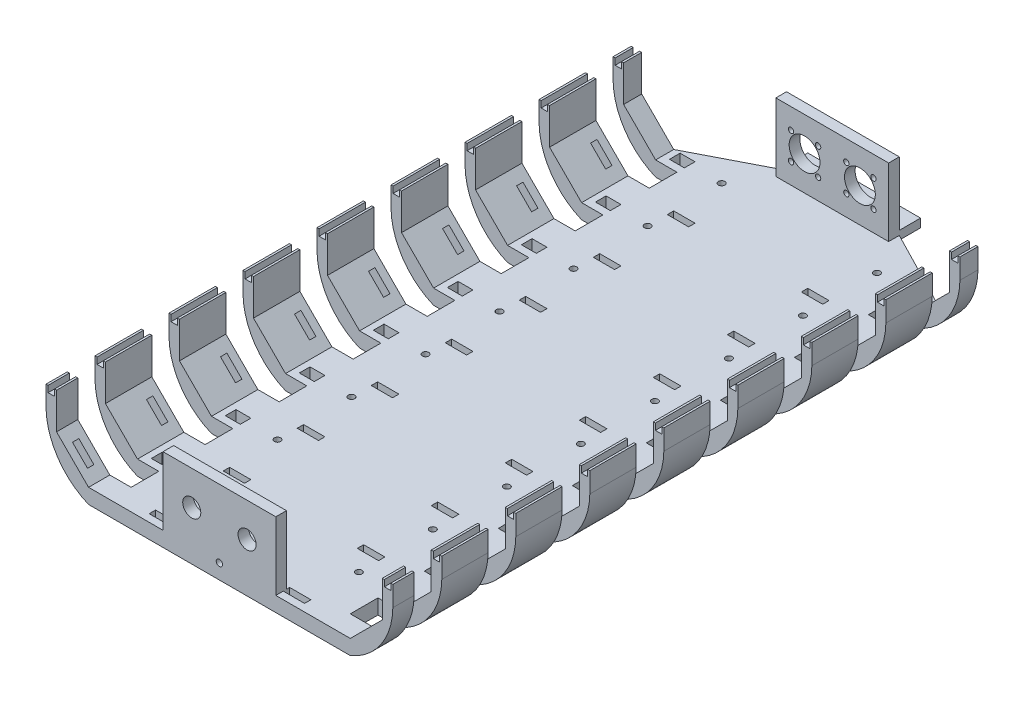
SolidWorks part; units mm, degrees
ref_plane "Front Plane" through (0, 0, 0) normal (0, 0, 1) x (1, 0, 0)
ref_plane "Top Plane" through (0, 0, 0) normal (0, 1, 0) x (1, 0, 0)
ref_plane "Right Plane" through (0, 0, 0) normal (1, 0, 0) x (0, 0, -1)
sketch "Sketch1" plane through (0, 0, 0) normal (0, 1, 0) x (1, 0, 0)
  line L0 (0, -135) -> (0, 135) construction
  line L1 (-13, 135) -> (-36, 135)
  line L2 (13, -135) -> (-13, -135)
  line L3 (13, -135) -> (13, 135) construction
  line L4 (13, 135) -> (-13, 135)
  line L5 (-13, -135) -> (-13, 135) construction
  line L8 (-36, 135) -> (-36, -135) construction
  line L9 (-36, -135) -> (-13, -135)
  line L10 (-36, 135) -> (-61.5, 135)
  line L11 (-61.5, 135) -> (-61.5, -135)
  line L12 (-61.5, -135) -> (-36, -135)
  line L13 (36, -135) -> (13, -135)
  line L14 (61.5, -135) -> (36, -135)
  line L15 (61.5, 135) -> (61.5, -135)
  line L16 (36, 135) -> (36, -135) construction
  line L17 (13, 135) -> (36, 135)
  line L18 (36, 135) -> (61.5, 135)
  point P0 (0, 0)
  point P4 (0, 0)
  dimension "D1" = 270
  dimension "D2" = 26
  dimension "D3" = 23
  dimension "D4" = 123
extrude "Boss-Extrude1" add sketch "Sketch1" along normal blind 7
sketch "Sketch2" plane through (0, 7, 0) normal (0, 1, 0) x (1, 0, 0)
  line L0 (61.5, -135) -> (61.5, 135) construction
  line L1 (-61.5, -135) -> (61.5, -135)
  line L2 (-61.5, -135) -> (-61.5, -130)
  line L3 (-61.5, -130) -> (61.5, -130)
  line L4 (61.5, -135) -> (61.5, -130)
  line L21 (-26.5, 130) -> (-26.5, -130) construction
  dimension "D1" = 5
extrude "Boss-Extrude2" add sketch "Sketch2" along normal blind 32
sketch "Sketch3" plane through (0, 0, 135) normal (0, 0, 1) x (1, 0, 0)
  line L0 (0, 39) -> (0, 0) construction
  line L2 (-61.5, 39) -> (-61.5, 7) construction
  line L3 (-61.5, 39) -> (61.5, 39) construction
  line L5 (-61.5, 39) -> (-61.5, 0) construction
  line L6 (-61.5, 23) -> (61.5, 23) construction
  line L7 (61.5, 39) -> (61.5, 0) construction
  circle A0 centre (-13, 23) radius 4.25
  circle A1 centre (13, 23) radius 4.25
  dimension "D1" = 8.5
  dimension "D2" = 8.5
  dimension "D3" = 26
  dimension "D4" = 13
  dimension "D5" = 32
  dimension "D6" = 16
sketch "Sketch9" plane through (0, 0, -135) normal (0, 0, -1) x (-1, 0, 0)
  line L1 (-61.5, 7) -> (61.5, 7)
  line L2 (-61.5, 7) -> (-61.5, 0)
  line L3 (-61.5, 0) -> (61.5, 0)
  line L4 (61.5, 7) -> (61.5, 0)
extrude "Boss-Extrude4" add sketch "Sketch9" along normal blind 5
sketch "Sketch13" plane through (0, 0, 135) normal (0, 0, 1) x (1, 0, 0)
  line L0 (-61.5, 39) -> (-61.5, 7)
  line L1 (-61.5, 39) -> (-61.5, 0) construction
  line L2 (-61.5, 39) -> (-26.5, 39)
  line L3 (-61.5, 39) -> (61.5, 39) construction
  line L4 (-26.5, 39) -> (-26.5, 7)
  line L5 (-26.5, 7) -> (-61.5, 7)
  line L6 (0, 39) -> (0, 5.5161) construction
  line L7 (26.5, 39) -> (26.5, 7)
  line L8 (61.5, 39) -> (26.5, 39)
  line L9 (61.5, 39) -> (61.5, 7)
  line L10 (26.5, 7) -> (61.5, 7)
  dimension "D1" = 32
  dimension "D2" = 35
extrude "Cut-Extrude5" cut sketch "Sketch13" against normal blind 11
sketch "Sketch14" plane through (0, 0, 135) normal (0, 0, 1) x (1, 0, 0)
  line L0 (0, 39) -> (0, 0) construction
  line L1 (-26.5, 39) -> (26.5, 39) construction
  line L2 (-81.5, 39) -> (0, 39) construction
  line L3 (-61.5, 0) -> (-81.5, 20) construction
  line L5 (-76.55, 22.05) -> (-61.5, 7)
  line L6 (-61.5, 0) -> (61.5, 0) construction
  line L7 (-61.5, 7) -> (-61.5, 0)
  line L12 (-81.5, 20) -> (-81.5, 39) construction
  line L13 (-81.5, 39) -> (-76.55, 39)
  line L14 (-76.55, 39) -> (-76.55, 22.05)
  line L21 (-61.5, 7) -> (-61.5, 39) construction
  line L22 (-81.5, 39) -> (-81.5, 29.5)
  line L23 (81.5, 39) -> (76.55, 39)
  line L24 (76.55, 39) -> (76.55, 22.05)
  line L25 (76.55, 22.05) -> (61.5, 7)
  line L26 (61.5, 7) -> (61.5, 0)
  line L27 (81.5, 39) -> (81.5, 29.5)
  arc A0 (-61.5, 0) -> (-81.5, 29.5) centre (-49.0062, 30) cw
  arc A1 (61.5, 0) -> (81.5, 29.5) centre (49.0062, 30) ccw
  dimension "D1" = 28.2843
  dimension "D2" = 45
  dimension "D3" = 4.95
  dimension "D4" = 20
  dimension "D5" = 4.9497
  dimension "D6" = 21.2839
  dimension "D7" = 30
  dimension "D8" = 9.5
extrude "Boss-Extrude10" add sketch "Sketch14" against normal blind 275
sketch "Sketch17" plane through (0, 7, 0) normal (0, 1, 0) x (1, 0, 0)
  line L0 (-26.5, 130) -> (26.5, 130) construction
  line L1 (0, 130) -> (0, 161) construction
  line L2 (-26.5, -135) -> (-26.5, 161) construction
  line L3 (26.5, -135) -> (26.5, 161) construction
  line L4 (26.5, 161) -> (-26.5, 161) construction
  line L5 (0, 161) -> (0, 226) construction
  line L6 (-61.5, 140) -> (-26.5, 226)
  line L7 (-26.5, 226) -> (0, 226)
  line L8 (0, 226) -> (26.5, 226)
  line L9 (26.5, 226) -> (61.5, 140)
  line L10 (26.5, 161) -> (26.5, 226) construction
  line L11 (-26.5, 161) -> (-26.5, 226) construction
  line L12 (-61.5, 140) -> (61.5, 140)
  line L13 (-61.5, 140) -> (61.5, 140) construction
  dimension "D1" = 31
  dimension "D2" = 296
  dimension "D3" = 90
  dimension "D4" = 65
  dimension "D5" = 10
extrude "Boss-Extrude13" add sketch "Sketch17" against normal blind 7 contours L12 L9 L8 L7 L6
sketch "Sketch18" plane through (0, 7, 0) normal (0, 1, 0) x (1, 0, 0)
  line L0 (-26.5, 127) -> (26.5, 127) construction
  line L1 (0, 127) -> (0, 158) construction
  line L2 (-26.5, 135) -> (-26.5, 158) construction
  line L3 (26.5, 132) -> (26.5, 158) construction
  line L4 (-26.5, 158) -> (-26.5, 153)
  line L5 (-26.5, 153) -> (26.5, 153)
  line L6 (26.5, 153) -> (26.5, 158)
  line L7 (26.5, 158) -> (-26.5, 158)
  line L8 (-61.5, 140) -> (-61.5, -135) construction
  line L9 (76.55, 140) -> (61.5, 140) construction
  dimension "D1" = 31
  dimension "D2" = 5
  dimension "D3" = 35
  dimension "D4" = 53
  dimension "D5" = 13
extrude "Boss-Extrude14" add sketch "Sketch18" along normal blind 32
extrude "Cut-Extrude8" cut sketch "Sketch3" against normal blind 334
sketch "Sketch19" plane through (0, 0, -153) normal (0, 0, 1) x (1, 0, 0)
  line L0 (0, 39) -> (0, 0) construction
  line L1 (-26.5, 39) -> (26.5, 39) construction
  line L3 (-6.636, 16.636) -> (-19.364, 16.636) construction
  line L4 (-6.636, 16.636) -> (-6.636, 29.364) construction
  line L5 (-6.636, 29.364) -> (-19.364, 29.364) construction
  line L6 (-19.364, 16.636) -> (-19.364, 29.364) construction
  line L7 (-6.636, 16.636) -> (-19.364, 29.364) construction
  line L8 (-6.636, 29.364) -> (-19.364, 16.636) construction
  circle A0 centre (-13, 23) radius 7.25
  circle A1 centre (-6.636, 16.636) radius 1.25
  circle A2 centre (-6.636, 29.364) radius 1.25
  circle A3 centre (-19.364, 29.364) radius 1.25
  circle A4 centre (-19.364, 16.636) radius 1.25
  circle A5 centre (13, 23) radius 7.25
  circle A6 centre (19.364, 16.636) radius 1.25
  circle A7 centre (6.636, 16.636) radius 1.25
  circle A8 centre (6.636, 29.364) radius 1.25
  circle A9 centre (19.364, 29.364) radius 1.25
  dimension "D1" = 14.5
  dimension "D4" = 2.5
  dimension "D5" = 2.5
  dimension "D6" = 2.5
  dimension "D7" = 2.5
  dimension "D2" = 18
  dimension "D3" = 18
  dimension "D8" = 12.7279
extrude "Cut-Extrude9" cut sketch "Sketch19" against normal blind 334
sketch "Sketch29" plane through (0, 7, 0) normal (0, 1, 0) x (1, 0, 0)
  line L0 (-61.5, 140) -> (-26.5, 158)
  line L1 (-26.5, 158) -> (26.5, 158)
  line L2 (26.5, 158) -> (61.5, 140)
  line L3 (61.5, 140) -> (26.5, 226)
  line L4 (26.5, 226) -> (-26.5, 226)
  line L5 (-26.5, 226) -> (-61.5, 140)
extrude "Cut-Extrude13" cut sketch "Sketch29" against normal blind 19
sketch "Sketch32" plane through (0, 7, 0) normal (0, 1, 0) x (1, 0, 0)
  line L0 (-61.5, 137.5) -> (-55, 137.5) construction
  line L1 (-61.5, 140) -> (-26.5, 140) construction
  line L3 (-61.5, 140) -> (-61.5, 130) construction
  line L4 (0, 158) -> (0, -135) construction
  line L5 (26.5, 158) -> (-26.5, 158) construction
  line L6 (-26.5, -135) -> (26.5, -135) construction
  line L7 (-61.5, 130) -> (-26.5, 130) construction
  line L8 (-81.5, 131.5) -> (-51.5, 131.5)
  line L9 (-26.5, 140) -> (-26.5, 130) construction
  line L10 (-81.5, 131.5) -> (-81.5, 118.5)
  line L11 (-51.5, 135) -> (-58.5, 135)
  line L12 (-51.5, 135) -> (-51.5, 140)
  line L13 (-51.5, 140) -> (-58.5, 140)
  line L14 (-58.5, 135) -> (-58.5, 140)
  line L15 (-51.5, 135) -> (-58.5, 140) construction
  line L16 (-51.5, 140) -> (-58.5, 135) construction
  line L23 (-81.5, 118.5) -> (-51.5, 118.5)
  line L24 (-51.5, 131.5) -> (-51.5, 118.5)
  line L25 (-81.5, 96.7143) -> (-81.5, 83.7143)
  line L26 (-81.5, 96.7143) -> (-51.5, 96.7143)
  line L27 (-51.5, 96.7143) -> (-51.5, 83.7143)
  line L28 (-81.5, 83.7143) -> (-51.5, 83.7143)
  line L29 (-51.5, 100.2143) -> (-51.5, 105.2143)
  line L30 (-51.5, 100.2143) -> (-58.5, 100.2143)
  line L31 (-58.5, 100.2143) -> (-58.5, 105.2143)
  line L32 (-51.5, 105.2143) -> (-58.5, 105.2143)
  line L37 (-81.5, 61.9286) -> (-81.5, 48.9286)
  line L38 (-81.5, 61.9286) -> (-51.5, 61.9286)
  line L39 (-51.5, 61.9286) -> (-51.5, 48.9286)
  line L40 (-81.5, 48.9286) -> (-51.5, 48.9286)
  line L41 (-51.5, 65.4286) -> (-51.5, 70.4286)
  line L42 (-51.5, 65.4286) -> (-58.5, 65.4286)
  line L43 (-58.5, 65.4286) -> (-58.5, 70.4286)
  line L44 (-51.5, 70.4286) -> (-58.5, 70.4286)
  line L49 (-81.5, 27.1429) -> (-81.5, 14.1429)
  line L50 (-81.5, 27.1429) -> (-51.5, 27.1429)
  line L51 (-51.5, 27.1429) -> (-51.5, 14.1429)
  line L52 (-81.5, 14.1429) -> (-51.5, 14.1429)
  line L53 (-51.5, 30.6429) -> (-51.5, 35.6429)
  line L54 (-51.5, 30.6429) -> (-58.5, 30.6429)
  line L55 (-58.5, 30.6429) -> (-58.5, 35.6429)
  line L56 (-51.5, 35.6429) -> (-58.5, 35.6429)
  line L61 (-81.5, -7.6429) -> (-81.5, -20.6429)
  line L62 (-81.5, -7.6429) -> (-51.5, -7.6429)
  line L63 (-51.5, -7.6429) -> (-51.5, -20.6429)
  line L64 (-81.5, -20.6429) -> (-51.5, -20.6429)
  line L65 (-51.5, -4.1429) -> (-51.5, 0.8571)
  line L66 (-51.5, -4.1429) -> (-58.5, -4.1429)
  line L67 (-58.5, -4.1429) -> (-58.5, 0.8571)
  line L68 (-51.5, 0.8571) -> (-58.5, 0.8571)
  line L73 (-81.5, -42.4286) -> (-81.5, -55.4286)
  line L74 (-81.5, -42.4286) -> (-51.5, -42.4286)
  line L75 (-51.5, -42.4286) -> (-51.5, -55.4286)
  line L76 (-81.5, -55.4286) -> (-51.5, -55.4286)
  line L77 (-51.5, -38.9286) -> (-51.5, -33.9286)
  line L78 (-51.5, -38.9286) -> (-58.5, -38.9286)
  line L79 (-58.5, -38.9286) -> (-58.5, -33.9286)
  line L80 (-51.5, -33.9286) -> (-58.5, -33.9286)
  line L85 (-81.5, -77.2143) -> (-81.5, -90.2143)
  line L86 (-81.5, -77.2143) -> (-51.5, -77.2143)
  line L87 (-51.5, -77.2143) -> (-51.5, -90.2143)
  line L88 (-81.5, -90.2143) -> (-51.5, -90.2143)
  line L89 (-51.5, -73.7143) -> (-51.5, -68.7143)
  line L90 (-51.5, -73.7143) -> (-58.5, -73.7143)
  line L91 (-58.5, -73.7143) -> (-58.5, -68.7143)
  line L92 (-51.5, -68.7143) -> (-58.5, -68.7143)
  line L97 (-81.5, -112) -> (-81.5, -125)
  line L98 (-81.5, -112) -> (-51.5, -112)
  line L99 (-51.5, -112) -> (-51.5, -125)
  line L100 (-81.5, -125) -> (-51.5, -125)
  line L101 (-51.5, -108.5) -> (-51.5, -103.5)
  line L102 (-51.5, -108.5) -> (-58.5, -108.5)
  line L103 (-58.5, -108.5) -> (-58.5, -103.5)
  line L104 (-51.5, -103.5) -> (-58.5, -103.5)
  line L109 (-26.5, -130) -> (-26.5, -125) construction
  line L110 (-26.5, -125) -> (-51.5, -125) construction
  line L111 (26.5, -125) -> (51.5, -125) construction
  line L112 (26.5, -130) -> (26.5, -125) construction
  line L115 (51.5, 140) -> (58.5, 135) construction
  line L116 (51.5, 135) -> (58.5, 140) construction
  line L117 (26.5, 140) -> (26.5, 130) construction
  line L118 (61.5, 130) -> (26.5, 130) construction
  line L119 (61.5, 140) -> (61.5, 130) construction
  line L120 (61.5, 140) -> (26.5, 140) construction
  line L121 (61.5, 137.5) -> (55, 137.5) construction
  line L126 (51.5, -103.5) -> (58.5, -103.5)
  line L127 (58.5, -108.5) -> (58.5, -103.5)
  line L128 (51.5, -108.5) -> (58.5, -108.5)
  line L129 (51.5, -108.5) -> (51.5, -103.5)
  line L130 (81.5, -125) -> (51.5, -125)
  line L131 (51.5, -112) -> (51.5, -125)
  line L132 (81.5, -112) -> (51.5, -112)
  line L133 (81.5, -112) -> (81.5, -125)
  line L138 (51.5, -68.7143) -> (58.5, -68.7143)
  line L139 (58.5, -73.7143) -> (58.5, -68.7143)
  line L140 (51.5, -73.7143) -> (58.5, -73.7143)
  line L141 (51.5, -73.7143) -> (51.5, -68.7143)
  line L142 (81.5, -90.2143) -> (51.5, -90.2143)
  line L143 (51.5, -77.2143) -> (51.5, -90.2143)
  line L144 (81.5, -77.2143) -> (51.5, -77.2143)
  line L145 (81.5, -77.2143) -> (81.5, -90.2143)
  line L150 (51.5, -33.9286) -> (58.5, -33.9286)
  line L151 (58.5, -38.9286) -> (58.5, -33.9286)
  line L152 (51.5, -38.9286) -> (58.5, -38.9286)
  line L153 (51.5, -38.9286) -> (51.5, -33.9286)
  line L154 (81.5, -55.4286) -> (51.5, -55.4286)
  line L155 (51.5, -42.4286) -> (51.5, -55.4286)
  line L156 (81.5, -42.4286) -> (51.5, -42.4286)
  line L157 (81.5, -42.4286) -> (81.5, -55.4286)
  line L162 (51.5, 0.8571) -> (58.5, 0.8571)
  line L163 (58.5, -4.1429) -> (58.5, 0.8571)
  line L164 (51.5, -4.1429) -> (58.5, -4.1429)
  line L165 (51.5, -4.1429) -> (51.5, 0.8571)
  line L166 (81.5, -20.6429) -> (51.5, -20.6429)
  line L167 (51.5, -7.6429) -> (51.5, -20.6429)
  line L168 (81.5, -7.6429) -> (51.5, -7.6429)
  line L169 (81.5, -7.6429) -> (81.5, -20.6429)
  line L174 (51.5, 35.6429) -> (58.5, 35.6429)
  line L175 (58.5, 30.6429) -> (58.5, 35.6429)
  line L176 (51.5, 30.6429) -> (58.5, 30.6429)
  line L177 (51.5, 30.6429) -> (51.5, 35.6429)
  line L178 (81.5, 14.1429) -> (51.5, 14.1429)
  line L179 (51.5, 27.1429) -> (51.5, 14.1429)
  line L180 (81.5, 27.1429) -> (51.5, 27.1429)
  line L181 (81.5, 27.1429) -> (81.5, 14.1429)
  line L186 (51.5, 70.4286) -> (58.5, 70.4286)
  line L187 (58.5, 65.4286) -> (58.5, 70.4286)
  line L188 (51.5, 65.4286) -> (58.5, 65.4286)
  line L189 (51.5, 65.4286) -> (51.5, 70.4286)
  line L190 (81.5, 48.9286) -> (51.5, 48.9286)
  line L191 (51.5, 61.9286) -> (51.5, 48.9286)
  line L192 (81.5, 61.9286) -> (51.5, 61.9286)
  line L193 (81.5, 61.9286) -> (81.5, 48.9286)
  line L198 (51.5, 105.2143) -> (58.5, 105.2143)
  line L199 (58.5, 100.2143) -> (58.5, 105.2143)
  line L200 (51.5, 100.2143) -> (58.5, 100.2143)
  line L201 (51.5, 100.2143) -> (51.5, 105.2143)
  line L202 (81.5, 83.7143) -> (51.5, 83.7143)
  line L203 (51.5, 96.7143) -> (51.5, 83.7143)
  line L204 (81.5, 96.7143) -> (51.5, 96.7143)
  line L205 (81.5, 96.7143) -> (81.5, 83.7143)
  line L206 (51.5, 131.5) -> (51.5, 118.5)
  line L207 (81.5, 118.5) -> (51.5, 118.5)
  line L212 (58.5, 135) -> (58.5, 140)
  line L213 (51.5, 140) -> (58.5, 140)
  line L214 (51.5, 135) -> (51.5, 140)
  line L215 (51.5, 135) -> (58.5, 135)
  line L216 (81.5, 131.5) -> (81.5, 118.5)
  line L217 (81.5, 131.5) -> (51.5, 131.5)
  line L218 (-81.5, 140) -> (-81.5, -135) construction
  circle A0 centre (-36.5, 137.5) radius 1.5
  circle A1 centre (-36.5, 102.7143) radius 1.5
  circle A2 centre (-36.5, 67.9286) radius 1.5
  circle A3 centre (-36.5, 33.1429) radius 1.5
  circle A4 centre (-36.5, -1.6429) radius 1.5
  circle A5 centre (-36.5, -36.4286) radius 1.5
  circle A6 centre (-36.5, -71.2143) radius 1.5
  circle A7 centre (-36.5, -106) radius 1.5
  circle A8 centre (36.5, -106) radius 1.5
  circle A9 centre (36.5, -71.2143) radius 1.5
  circle A10 centre (36.5, -36.4286) radius 1.5
  circle A11 centre (36.5, -1.6429) radius 1.5
  circle A12 centre (36.5, 33.1429) radius 1.5
  circle A13 centre (36.5, 67.9286) radius 1.5
  circle A14 centre (36.5, 102.7143) radius 1.5
  circle A15 centre (36.5, 137.5) radius 1.5
  dimension "D7" = 3
  dimension "D1" = 10
  dimension "D2" = 35
  dimension "D3" = 5
  dimension "D4" = 7
  dimension "D5" = 3
  dimension "D6" = 2.5
  dimension "D8" = 25
  dimension "D9" = 2.5
  dimension "D10" = 3.5
  dimension "D15" = 13
  dimension "D17" = 5
  dimension "D16" = 8
extrude "Cut-Extrude16" cut sketch "Sketch32" against normal through all both and the other way through all
sketch "Sketch33" plane through (0, 7, 0) normal (0, 1, 0) x (1, 0, 0)
  line L0 (-61.5, 118.5) -> (-26.5, 118.5) construction
  line L1 (-26.5, 118.5) -> (-26.5, 115) construction
  line L2 (0, 158) -> (0, -135) construction
  line L3 (-26.5, 115) -> (-36.5, 115)
  line L4 (-26.5, 115) -> (-26.5, 112)
  line L5 (-26.5, 112) -> (-36.5, 112)
  line L6 (-36.5, 115) -> (-36.5, 112)
  line L7 (26.5, 158) -> (-26.5, 158) construction
  line L8 (-26.5, -135) -> (26.5, -135) construction
  line L9 (-26.5, 80.2143) -> (-26.5, 77.2143)
  line L10 (-26.5, 80.2143) -> (-36.5, 80.2143)
  line L11 (-36.5, 80.2143) -> (-36.5, 77.2143)
  line L12 (-26.5, 77.2143) -> (-36.5, 77.2143)
  line L13 (-26.5, 45.4286) -> (-26.5, 42.4286)
  line L14 (-26.5, 45.4286) -> (-36.5, 45.4286)
  line L15 (-36.5, 45.4286) -> (-36.5, 42.4286)
  line L16 (-26.5, 42.4286) -> (-36.5, 42.4286)
  line L17 (-26.5, 10.6429) -> (-26.5, 7.6429)
  line L18 (-26.5, 10.6429) -> (-36.5, 10.6429)
  line L19 (-36.5, 10.6429) -> (-36.5, 7.6429)
  line L20 (-26.5, 7.6429) -> (-36.5, 7.6429)
  line L21 (-26.5, -24.1429) -> (-26.5, -27.1429)
  line L22 (-26.5, -24.1429) -> (-36.5, -24.1429)
  line L23 (-36.5, -24.1429) -> (-36.5, -27.1429)
  line L24 (-26.5, -27.1429) -> (-36.5, -27.1429)
  line L25 (-26.5, -58.9286) -> (-26.5, -61.9286)
  line L26 (-26.5, -58.9286) -> (-36.5, -58.9286)
  line L27 (-36.5, -58.9286) -> (-36.5, -61.9286)
  line L28 (-26.5, -61.9286) -> (-36.5, -61.9286)
  line L29 (-26.5, -93.7143) -> (-26.5, -96.7143)
  line L30 (-26.5, -93.7143) -> (-36.5, -93.7143)
  line L31 (-36.5, -93.7143) -> (-36.5, -96.7143)
  line L32 (-26.5, -96.7143) -> (-36.5, -96.7143)
  line L33 (-26.5, -128.5) -> (-26.5, -131.5)
  line L34 (-26.5, -128.5) -> (-36.5, -128.5)
  line L35 (-36.5, -128.5) -> (-36.5, -131.5)
  line L36 (-26.5, -131.5) -> (-36.5, -131.5)
  line L37 (-51.5, -125) -> (-51.5, -128.5) construction
  line L38 (-51.5, -128.5) -> (-16.5, -128.5) construction
  line L39 (26.5, -128.5) -> (36.5, -128.5)
  line L40 (36.5, -128.5) -> (36.5, -131.5)
  line L41 (26.5, -131.5) -> (36.5, -131.5)
  line L42 (26.5, -128.5) -> (26.5, -131.5)
  line L43 (26.5, -93.7143) -> (36.5, -93.7143)
  line L44 (36.5, -93.7143) -> (36.5, -96.7143)
  line L45 (26.5, -96.7143) -> (36.5, -96.7143)
  line L46 (26.5, -93.7143) -> (26.5, -96.7143)
  line L47 (26.5, -58.9286) -> (36.5, -58.9286)
  line L48 (36.5, -58.9286) -> (36.5, -61.9286)
  line L49 (26.5, -61.9286) -> (36.5, -61.9286)
  line L50 (26.5, -58.9286) -> (26.5, -61.9286)
  line L51 (26.5, -24.1429) -> (36.5, -24.1429)
  line L52 (36.5, -24.1429) -> (36.5, -27.1429)
  line L53 (26.5, -27.1429) -> (36.5, -27.1429)
  line L54 (26.5, -24.1429) -> (26.5, -27.1429)
  line L55 (26.5, 10.6429) -> (36.5, 10.6429)
  line L56 (36.5, 10.6429) -> (36.5, 7.6429)
  line L57 (26.5, 7.6429) -> (36.5, 7.6429)
  line L58 (26.5, 10.6429) -> (26.5, 7.6429)
  line L59 (26.5, 45.4286) -> (36.5, 45.4286)
  line L60 (36.5, 45.4286) -> (36.5, 42.4286)
  line L61 (26.5, 42.4286) -> (36.5, 42.4286)
  line L62 (26.5, 45.4286) -> (26.5, 42.4286)
  line L63 (26.5, 80.2143) -> (36.5, 80.2143)
  line L64 (36.5, 80.2143) -> (36.5, 77.2143)
  line L65 (26.5, 77.2143) -> (36.5, 77.2143)
  line L66 (26.5, 80.2143) -> (26.5, 77.2143)
  line L67 (26.5, 112) -> (36.5, 112)
  line L68 (36.5, 115) -> (36.5, 112)
  line L69 (26.5, 115) -> (36.5, 115)
  line L70 (26.5, 115) -> (26.5, 112)
  dimension "D1" = 35
  dimension "D2" = 3.5
  dimension "D3" = 3
  dimension "D4" = 10
  dimension "D6" = 3.5
  dimension "D7" = 35
  dimension "D5" = 8
extrude "Cut-Extrude18" cut sketch "Sketch33" against normal blind 4.5
sketch "Sketch34" plane through (27.25, -27.25, 0) normal (-0.7071, 0.7071, 0) x (0, 0, 1)
  line L0 (-118.5, 59.0788) -> (-96.7143, 59.0788) construction
  line L1 (-118.5, 48.4368) -> (-118.5, 69.7207) construction
  line L2 (-96.7143, 69.7207) -> (-96.7143, 48.4368) construction
  line L3 (-113.5, 69.7207) -> (-113.5, 48.4368) construction
  line L4 (-118.5, 69.7207) -> (-96.7143, 69.7207) construction
  line L5 (-96.7143, 48.4368) -> (-118.5, 48.4368) construction
  line L6 (-77.2143, 54.0788) -> (-77.2143, 64.0788)
  line L7 (-112, 54.0788) -> (-115, 54.0788)
  line L8 (-112, 54.0788) -> (-112, 64.0788)
  line L9 (-112, 64.0788) -> (-115, 64.0788)
  line L10 (-115, 54.0788) -> (-115, 64.0788)
  line L11 (-112, 54.0788) -> (-115, 64.0788) construction
  line L12 (-112, 64.0788) -> (-115, 54.0788) construction
  line L13 (-77.2143, 54.0788) -> (-80.2143, 54.0788)
  line L14 (-80.2143, 54.0788) -> (-80.2143, 64.0788)
  line L15 (-77.2143, 64.0788) -> (-80.2143, 64.0788)
  line L16 (-42.4286, 54.0788) -> (-42.4286, 64.0788)
  line L17 (-42.4286, 54.0788) -> (-45.4286, 54.0788)
  line L18 (-45.4286, 54.0788) -> (-45.4286, 64.0788)
  line L19 (-42.4286, 64.0788) -> (-45.4286, 64.0788)
  line L20 (-7.6429, 54.0788) -> (-7.6429, 64.0788)
  line L21 (-7.6429, 54.0788) -> (-10.6429, 54.0788)
  line L22 (-10.6429, 54.0788) -> (-10.6429, 64.0788)
  line L23 (-7.6429, 64.0788) -> (-10.6429, 64.0788)
  line L24 (27.1429, 54.0788) -> (27.1429, 64.0788)
  line L25 (27.1429, 54.0788) -> (24.1429, 54.0788)
  line L26 (24.1429, 54.0788) -> (24.1429, 64.0788)
  line L27 (27.1429, 64.0788) -> (24.1429, 64.0788)
  line L28 (61.9286, 54.0788) -> (61.9286, 64.0788)
  line L29 (61.9286, 54.0788) -> (58.9286, 54.0788)
  line L30 (58.9286, 54.0788) -> (58.9286, 64.0788)
  line L31 (61.9286, 64.0788) -> (58.9286, 64.0788)
  line L32 (96.7143, 54.0788) -> (96.7143, 64.0788)
  line L33 (96.7143, 54.0788) -> (93.7143, 54.0788)
  line L34 (93.7143, 54.0788) -> (93.7143, 64.0788)
  line L35 (96.7143, 64.0788) -> (93.7143, 64.0788)
  line L36 (131.5, 54.0788) -> (131.5, 64.0788)
  line L37 (131.5, 54.0788) -> (128.5, 54.0788)
  line L38 (128.5, 54.0788) -> (128.5, 64.0788)
  line L39 (131.5, 64.0788) -> (128.5, 64.0788)
  line L40 (125, 59.0788) -> (135, 59.0788) construction
  line L41 (125, 48.4368) -> (125, 69.7207) construction
  line L42 (135, 69.7207) -> (135, 48.4368) construction
  line L43 (128.5, 48.4368) -> (128.5, 69.7207) construction
  line L44 (135, 48.4368) -> (125, 48.4368) construction
  line L45 (125, 69.7207) -> (135, 69.7207) construction
  point P12 (-113.5, 59.0788)
  dimension "D1" = 5
  dimension "D2" = 3
  dimension "D3" = 10
  dimension "D5" = 3.5
  dimension "D4" = 8
extrude "Cut-Extrude19" cut sketch "Sketch34" against normal blind 4.5
mirror "Mirror1" about plane through (0, 0, 0) normal (1, 0, 0) of "Cut-Extrude19"
sketch "Sketch35" plane through (0, 39, 0) normal (0, 1, 0) x (1, 0, 0)
  line L0 (-79.025, 140) -> (-79.025, -135) construction
  line L1 (-76.55, 140) -> (-81.5, 140) construction
  line L2 (-76.55, -135) -> (-81.5, -135) construction
  line L3 (-80.525, -135) -> (-77.525, -135)
  line L4 (-80.525, -135) -> (-80.525, 140)
  line L5 (-80.525, 140) -> (-77.525, 140)
  line L6 (-77.525, 140) -> (-77.525, -135)
  line L7 (0, -135) -> (0, 158) construction
  line L8 (-26.5, -135) -> (26.5, -135) construction
  line L9 (26.5, 158) -> (-26.5, 158) construction
  line L10 (80.525, 140) -> (77.525, 140)
  line L11 (80.525, -135) -> (80.525, 140)
  line L12 (80.525, -135) -> (77.525, -135)
  line L13 (77.525, 140) -> (77.525, -135)
  point P8 (-79.025, -135)
  dimension "D1" = 1.5
extrude "Cut-Extrude20" cut sketch "Sketch35" against normal blind 3
sketch "Sketch36" plane through (0, 0, -158) normal (0, 0, -1) x (-1, 0, 0)
  line L5 (-26.5, 39) -> (-26.5, 7) construction
  line L6 (-26.5, 9.0853) -> (26.5, 9.0853)
  line L7 (-26.5, 9.0853) -> (-26.5, 5.0853)
  line L8 (-26.5, 5.0853) -> (26.5, 5.0853)
  line L9 (26.5, 9.0853) -> (26.5, 5.0853)
  line L10 (26.5, 0) -> (26.5, 7) construction
  line L11 (-26.5, 5.0853) -> (26.5, 5.0853) construction
  dimension "D1" = 4
extrude "Boss-Extrude15" add sketch "Sketch36" along normal blind 10
sketch "Sketch37" plane through (0, 0, 135) normal (0, 0, 1) x (1, 0, 0)
  line L0 (-26.5, 7) -> (26.5, 7) construction
  circle A0 centre (0, 7) radius 1.5
  dimension "D1" = 3
extrude "Cut-Extrude21" cut sketch "Sketch37" against normal blind 10 contours A0
